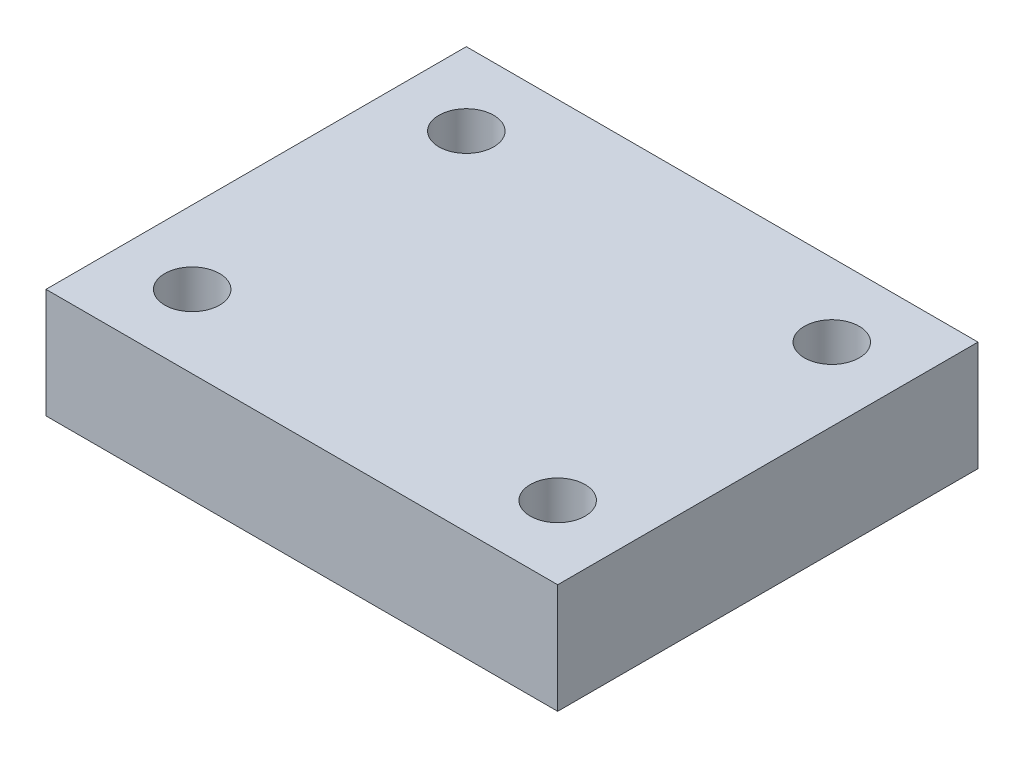
SolidWorks part; units mm, degrees
material "6061-T6 (SS)"
ref_plane "前视基准面" through (0, 0, 0) normal (0, 0, 1) x (1, 0, 0)
ref_plane "上视基准面" through (0, 0, 0) normal (0, 1, 0) x (1, 0, 0)
ref_plane "右视基准面" through (0, 0, 0) normal (1, 0, 0) x (0, 0, -1)
sketch "草图1" plane through (0, 0, 0) normal (0, 1, 0) x (1, 0, 0)
  line L5 (-10, 7.5) -> (10, 7.5) construction
  line L6 (-10, 7.5) -> (-10, -7.5) construction
  line L7 (14, 11.5) -> (-14, 11.5)
  line L8 (14, 11.5) -> (14, -11.5)
  line L9 (14, -11.5) -> (-14, -11.5)
  line L10 (-14, 11.5) -> (-14, -11.5)
  line L11 (0, -11.5) -> (0, 11.5) construction
  line L12 (14, 0) -> (-14, 0) construction
  line L13 (-10, -7.5) -> (10, -7.5) construction
  line L14 (10, 7.5) -> (10, -7.5) construction
  line L15 (0, -7.5) -> (0, 7.5) construction
  line L16 (-10, 0) -> (10, 0) construction
  circle A4 centre (-10, 7.5) radius 1.5
  circle A5 centre (10, 7.5) radius 1.5
  circle A6 centre (10, -7.5) radius 1.5
  circle A7 centre (-10, -7.5) radius 1.5
  point P0 (0, 0)
  point P1 (0, 0)
  point P8 (0, 0)
  dimension "D3" = 15
  dimension "D5" = 3
  dimension "D1" = 23
  dimension "D2" = 28
  dimension "D4" = 20
extrude "凸台-拉伸1" add sketch "草图1" along normal blind 6
cosmetic thread "装饰螺纹线3"
cosmetic thread "装饰螺纹线4"
cosmetic thread "装饰螺纹线6"
cosmetic thread "装饰螺纹线7"
sketch "草图2" plane through (0, 0, 11.5) normal (0, 0, 1) x (1, 0, 0)
  line L0 (-14, 0) -> (-5.3918, -17.6323)
  line L1 (-14, 0) -> (14, 0)
  line L2 (14, 0) -> (5.3918, -17.6323)
  line L3 (0, 0) -> (0, -50000) construction
  circle A1 centre (0, -15) radius 2.5
  arc A2 (-5.3918, -17.6323) -> (5.3918, -17.6323) centre (0, -15) ccw
  point P7 (0, 0)
  dimension "D1" = 12
  dimension "D4" = 5
  dimension "D2" = 15
extrude "凸台-拉伸2" [suppressed] add sketch "草图2" against normal blind 8
cosmetic thread "装饰螺纹线5" [suppressed] parameters "D2"=6
